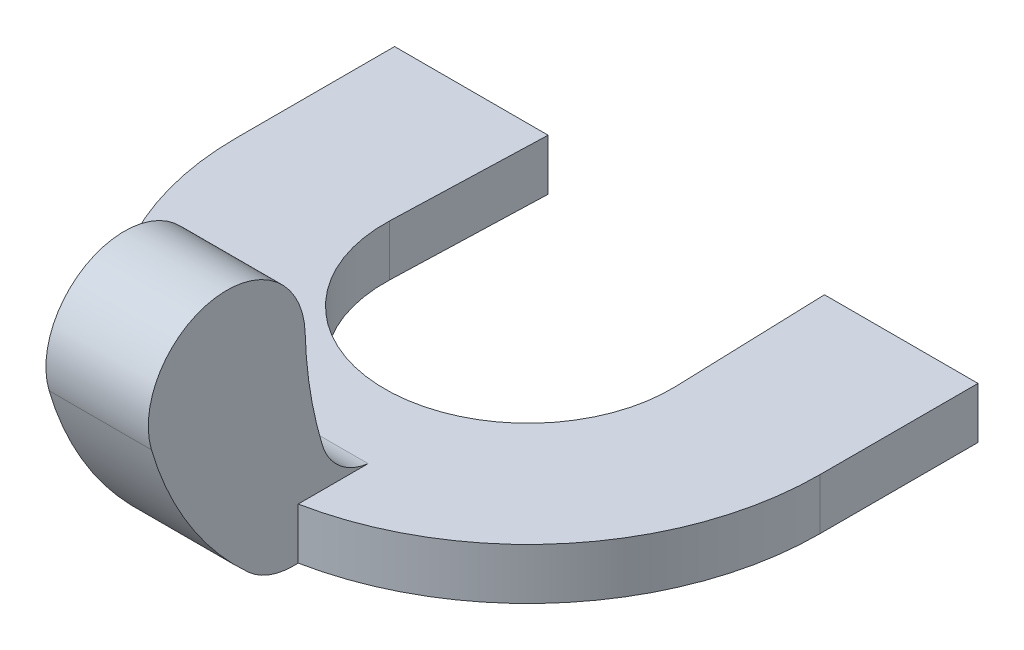
SolidWorks part; units mm, degrees
ref_plane "Front Plane" through (0, 0, 0) normal (0, 0, 1) x (1, 0, 0)
ref_plane "Top Plane" through (0, 0, 0) normal (0, 1, 0) x (1, 0, 0)
ref_plane "Right Plane" through (0, 0, 0) normal (1, 0, 0) x (0, 0, -1)
sketch "Sketch1" plane through (0, 0, 0) normal (0, 1, 0) x (1, 0, 0)
  line L0 (0, 0) -> (-3, 0)
  line L1 (-3, 0) -> (-3, -3.0903)
  line L2 (8.4, -3.0903) -> (8.4, 0)
  line L3 (8.4, 0) -> (5.4, 0)
  line L4 (5.4, 0) -> (5.4985, -2.9984)
  line L5 (-0.0985, -2.9984) -> (0, 0)
  arc A0 (-3, -3.0903) -> (8.4, -3.0903) centre (2.7, -3.0903) ccw
  arc A1 (5.4985, -2.9984) -> (-0.0985, -2.9984) centre (2.7, -3.0903) cw
  dimension "D1" = 2.8
  dimension "D2" = 3
  dimension "D3" = 3
  dimension "D4" = 5.4
extrude "Boss-Extrude1" add sketch "Sketch1" along normal blind 1
sketch "Sketch2" plane through (0, 0, 0) normal (1, 0, 0) x (0, 0, -1)
  line L0 (-6.3352, 0) -> (-8.7903, 0)
  line L1 (-8.7903, 0) -> (-3.0903, 0) construction
  line L2 (-3.0903, 1) -> (-8.7903, 1) construction
  line L3 (-7.3161, 1) -> (-6.3352, 1)
  line L4 (-6.3352, 1) -> (-6.3352, 0)
  arc A0 (-8.7903, 0) -> (-9.6565, 0.3338) centre (-8.7903, 1.2907) cw
  arc A1 (-9.6565, 0.3338) -> (-11.5503, 3.3507) centre (-5.2482, 5.2038) cw
  arc A2 (-11.5503, 3.3507) -> (-8.5477, 3.8289) centre (-10.0798, 3.7831) cw
  arc A3 (-8.5477, 3.8289) -> (-8.2099, 1.7562) centre (-0.5513, 4.0683) ccw
  arc A4 (-8.2099, 1.7562) -> (-7.3161, 1) centre (-7.18, 2.0671) ccw
extrude "Boss-Extrude2" add sketch "Sketch2" along normal blind 1 and the other way blind 1 from offset 2.8
